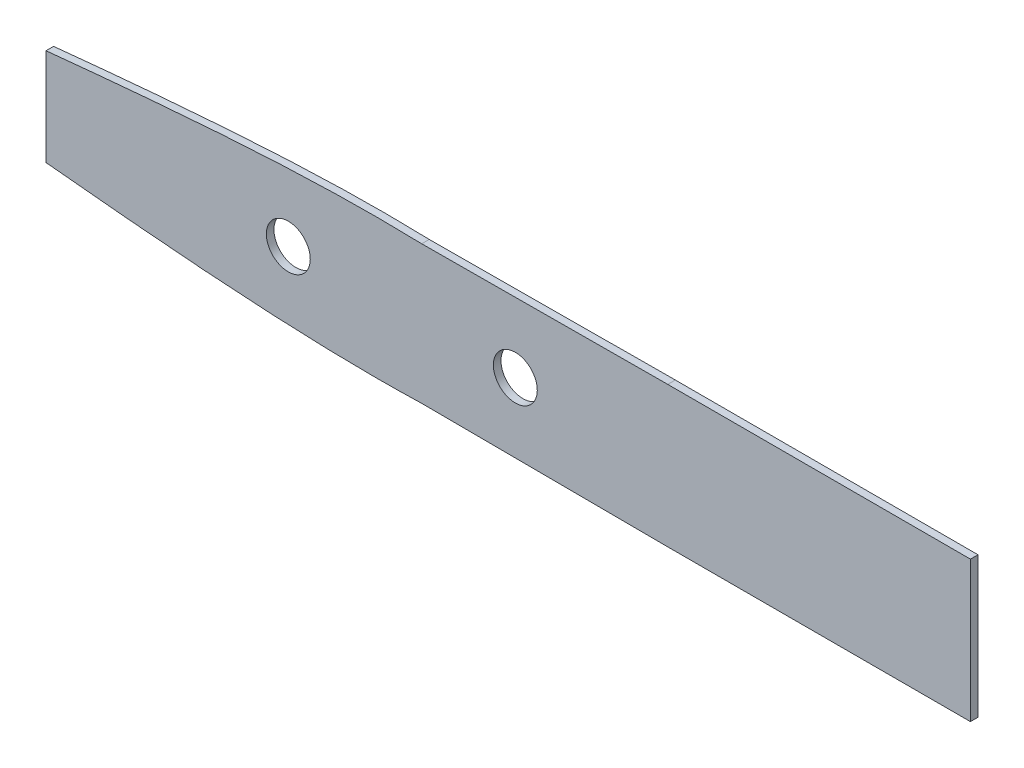
SolidWorks part; units mm, degrees
material "Thornel Mat VMA"
ref_plane "Front Plane" through (0, 0, 0) normal (0, 0, 1) x (1, 0, 0)
ref_plane "Top Plane" through (0, 0, 0) normal (0, 1, 0) x (1, 0, 0)
ref_plane "Right Plane" through (0, 0, 0) normal (1, 0, 0) x (0, 0, -1)
sketch "Sketch1" plane through (0, 0, 0) normal (0, 0, 1) x (1, 0, 0)
  line L0 (-67.9287, 11.1658) -> (-67.9287, -5.095)
  line L1 (-4.8766, -8.56) -> (36.4145, -8.7756)
  line L2 (36.4145, -8.7756) -> (36.4145, 14.8464)
  line L3 (36.4145, 14.8464) -> (-4.8766, 14.6308)
  line L4 (-67.9287, 3.0354) -> (36.4145, 3.0354) construction
  line L5 (36.4145, 14.8464) -> (87.2145, 14.8464)
  line L6 (87.2145, 14.8464) -> (87.2145, -8.7756)
  line L7 (87.2145, -8.7756) -> (36.4145, -8.7756)
  circle A0 centre (10.8367, 3.0354) radius 3.683
  circle A1 centre (-27.2633, 3.0354) radius 3.683
  spline S0 degree 3 poles (-4.8766, 14.6308) (-5.2195, 14.6418) (-8.2305, 14.7312) (-14.0815, 14.7833) (-22.5753, 14.6119) (-31.5063, 14.2085) (-40.7999, 13.6035) (-50.3705, 12.8346) (-59.445, 12.0062) (-65.3172, 11.4281) (-67.9287, 11.1658) knots 0.21972 0.21972 0.21972 0.21972 0.222404 0.243281 0.265482 0.28885 0.313208 0.33833 0.363954 0.384485 0.384485 0.384485 0.384485
  spline S1 degree 3 poles (-67.9287, -5.095) (-65.3172, -5.3573) (-59.445, -5.9354) (-50.3705, -6.7638) (-40.7999, -7.5327) (-31.5063, -8.1377) (-22.5753, -8.5411) (-14.0815, -8.7125) (-8.2305, -8.6604) (-5.2195, -8.571) (-4.8766, -8.56) knots 0.615515 0.615515 0.615515 0.615515 0.636046 0.66167 0.686792 0.71115 0.734518 0.756719 0.777596 0.78028 0.78028 0.78028 0.78028
  dimension "D1" = 25.5778
  dimension "D2" = 38.1
  dimension "D3" = 11.5954
  dimension "D4" = 11.5954
  dimension "D5" = 23.622
  dimension "D6" = 50.8
extrude "Boss-Extrude1" add sketch "Sketch1" along normal blind 1.27 contours L0 L4 A1 A0 L2 L3 S0 | L4 L0 S1 L1 L2 A0 A1 | L7 L6 L5 L2
